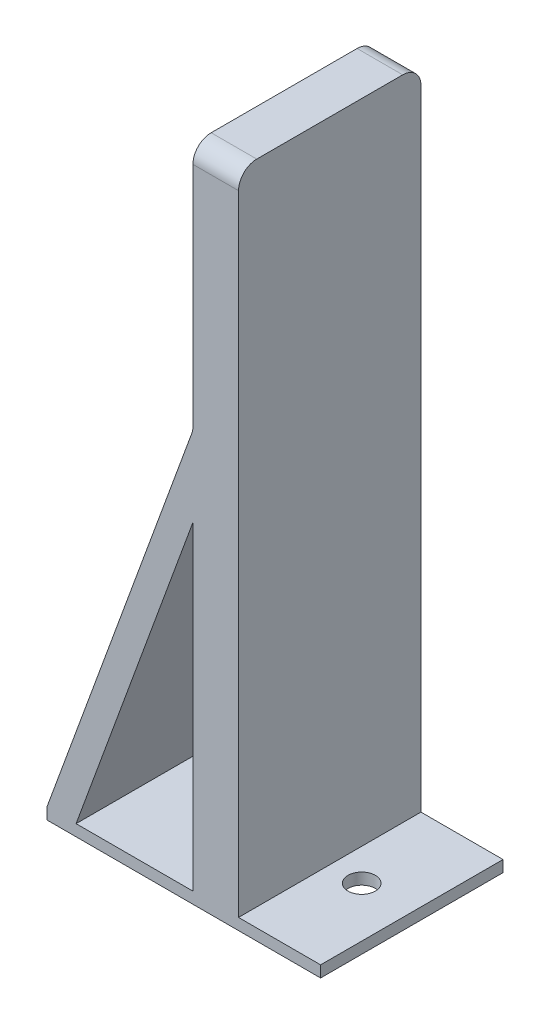
SolidWorks part; units mm, degrees
ref_plane "Front Plane" through (0, 0, 0) normal (0, 0, 1) x (1, 0, 0)
ref_plane "Top Plane" through (0, 0, 0) normal (0, 1, 0) x (1, 0, 0)
ref_plane "Right Plane" through (0, 0, 0) normal (1, 0, 0) x (0, 0, -1)
sketch "Sketch1" plane through (0, 0, 0) normal (0, 1, 0) x (1, 0, 0)
  line L1 (-15, -10) -> (15, -10)
  line L2 (-15, -10) -> (-15, 10)
  line L3 (-15, 10) -> (15, 10)
  line L4 (15, -10) -> (15, 10)
  line L5 (0, 10) -> (0, -10) construction
  line L6 (-15, 0) -> (15, 0) construction
  point P0 (0, 0)
  dimension "D1" = 20
  dimension "D2" = 30
extrude "Boss-Extrude1" add sketch "Sketch1" along normal blind 1.25
sketch "Sketch2" plane through (0, 1.25, 0) normal (0, 1, 0) x (1, 0, 0)
  line L0 (1, 10) -> (1, -10)
  line L1 (15, 10) -> (-15, 10) construction
  line L2 (-15, -10) -> (15, -10) construction
  line L3 (1, -10) -> (6, -10)
  line L4 (6, -10) -> (6, 10)
  line L5 (6, 10) -> (1, 10)
  line L7 (-15, 10) -> (-15, -10) construction
  dimension "D1" = 21
  dimension "D2" = 5
extrude "Boss-Extrude2" add sketch "Sketch2" along normal blind 71
sketch "Sketch3" plane through (0, 0, 10) normal (0, 0, 1) x (1, 0, 0)
  line L0 (1, 36.25) -> (-11.8055, 1.25)
  line L1 (-15, 1.25) -> (1, 44.9812)
  line L2 (1, 72.25) -> (1, 1.25) construction
  line L3 (-15, 1.25) -> (1, 1.25) construction
  line L4 (1, 44.9812) -> (1, 36.25)
  line L5 (-15, 1.25) -> (-11.8055, 1.25)
  dimension "D1" = 3
  dimension "D2" = 35
extrude "Boss-Extrude3" add sketch "Sketch3" against normal up to surface (20 mm away) up to face at (1.75, 18.6875, -10)
sketch "Sketch4" plane through (0, 1.25, 0) normal (0, 1, 0) x (1, 0, 0)
  line L0 (-15, 10) -> (-15, -10) construction
  circle A0 centre (9.5, 0) radius 1.5
  dimension "D2" = 3
  dimension "D1" = 24.5
extrude "Cut-Extrude2" cut sketch "Sketch4" against normal up to next
fillet "Fillet1" radius 2 3 edges at (3.5, 72.25, -10) (3.5, 72.25, 10) (1, 44.9812, 0)
